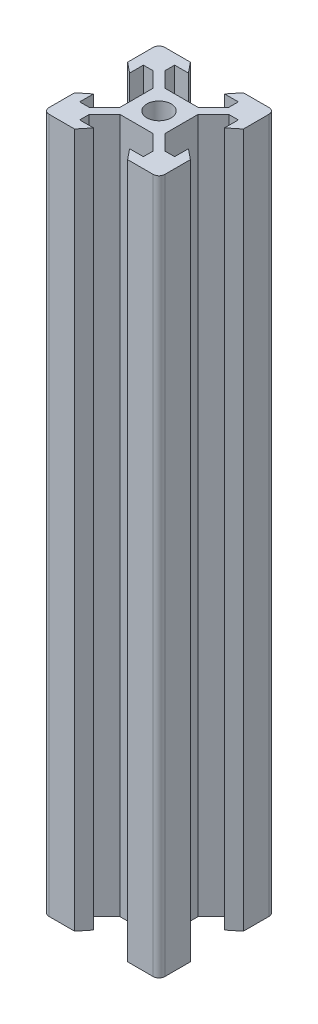
SolidWorks part; units mm, degrees
ref_plane "Front Plane" through (0, 0, 0) normal (0, 0, 1) x (1, 0, 0)
ref_plane "Top Plane" through (0, 0, 0) normal (0, 1, 0) x (1, 0, 0)
ref_plane "Right Plane" through (0, 0, 0) normal (1, 0, 0) x (0, 0, -1)
sketch "Sketch1" plane through (0, 0, 0) normal (0, 1, 0) x (1, 0, 0)
  line L0 (-3.125, 8.2) -> (-4.58, 10)
  line L1 (-9, 10) -> (9, 10)
  line L2 (-10, 9) -> (-10, -9)
  line L3 (-9, -10) -> (9, -10)
  line L4 (10, 9) -> (10, -9)
  line L5 (-10, 10) -> (10, -10) construction
  line L6 (-10, -10) -> (10, 10) construction
  line L7 (-10, 0) -> (0, 0) construction
  line L8 (0, 10) -> (0, 0) construction
  line L9 (-8.2, 3.125) -> (-10, 4.58)
  line L10 (-8.2, 3.125) -> (-8.2, 5.5)
  line L11 (-3.125, 8.2) -> (-5.5, 8.2)
  line L12 (-5.5, 8.2) -> (-5.5, 6.56)
  line L13 (-2.84, 3.9) -> (2.84, 3.9)
  line L14 (-5.5, 6.56) -> (-2.84, 3.9)
  line L15 (-8.2, 5.5) -> (-6.56, 5.5)
  line L16 (-6.56, 5.5) -> (-3.9, 2.84)
  line L17 (-3.9, 2.84) -> (-3.9, -2.84)
  line L18 (3.9, 2.84) -> (3.9, -2.84)
  line L19 (6.56, 5.5) -> (3.9, 2.84)
  line L20 (8.2, 5.5) -> (6.56, 5.5)
  line L21 (8.2, 3.125) -> (8.2, 5.5)
  line L22 (8.2, 3.125) -> (10, 4.58)
  line L23 (3.125, 8.2) -> (4.58, 10)
  line L24 (3.125, 8.2) -> (5.5, 8.2)
  line L25 (5.5, 8.2) -> (5.5, 6.56)
  line L26 (5.5, 6.56) -> (2.84, 3.9)
  line L27 (-8.2, -3.125) -> (-10, -4.58)
  line L28 (-8.2, -3.125) -> (-8.2, -5.5)
  line L29 (-8.2, -5.5) -> (-6.56, -5.5)
  line L30 (-6.56, -5.5) -> (-3.9, -2.84)
  line L31 (8.2, -3.125) -> (10, -4.58)
  line L32 (8.2, -3.125) -> (8.2, -5.5)
  line L33 (8.2, -5.5) -> (6.56, -5.5)
  line L34 (6.56, -5.5) -> (3.9, -2.84)
  line L35 (5.5, -6.56) -> (2.84, -3.9)
  line L36 (5.5, -8.2) -> (5.5, -6.56)
  line L37 (3.125, -8.2) -> (5.5, -8.2)
  line L38 (3.125, -8.2) -> (4.58, -10)
  line L39 (-5.5, -6.56) -> (-2.84, -3.9)
  line L40 (-2.84, -3.9) -> (2.84, -3.9)
  line L41 (-5.5, -8.2) -> (-5.5, -6.56)
  line L42 (-3.125, -8.2) -> (-5.5, -8.2)
  line L43 (-3.125, -8.2) -> (-4.58, -10)
  circle A0 centre (0, 0) radius 2.1
  arc A1 (-10, -9) -> (-9, -10) centre (-9, -9) ccw
  arc A2 (9, -10) -> (10, -9) centre (9, -9) ccw
  arc A3 (9, 10) -> (10, 9) centre (9, 9) cw
  arc A4 (-9, 10) -> (-10, 9) centre (-9, 9) ccw
  point P0 (0, 0)
  point P35 (0, 3.9)
  point P40 (-3.9, 0)
  point P41 (3.9, 0)
  dimension "D3" = 4.2
  dimension "D2" = 1
  dimension "D1" = 20
  dimension "D4" = 6.1
  dimension "D5" = 6.25
  dimension "D6" = 11
  dimension "D7" = 5.68
  dimension "D8" = 9.16
  dimension "D9" = 1.8
extrude "Boss-Extrude1" add sketch "Sketch1" along normal blind 120 contours L43 L42 L41 L39 L40 L35 L36 L37 L38 L3 L4 L31 L32 L33 L34 L18 L19 L20 L21 L22 L1 L23 L24 L25 L26 L13 L14 L12 L11 L0 L2 L9 L10 L15 L16 L17 L30 L29 L28 L27 A0
